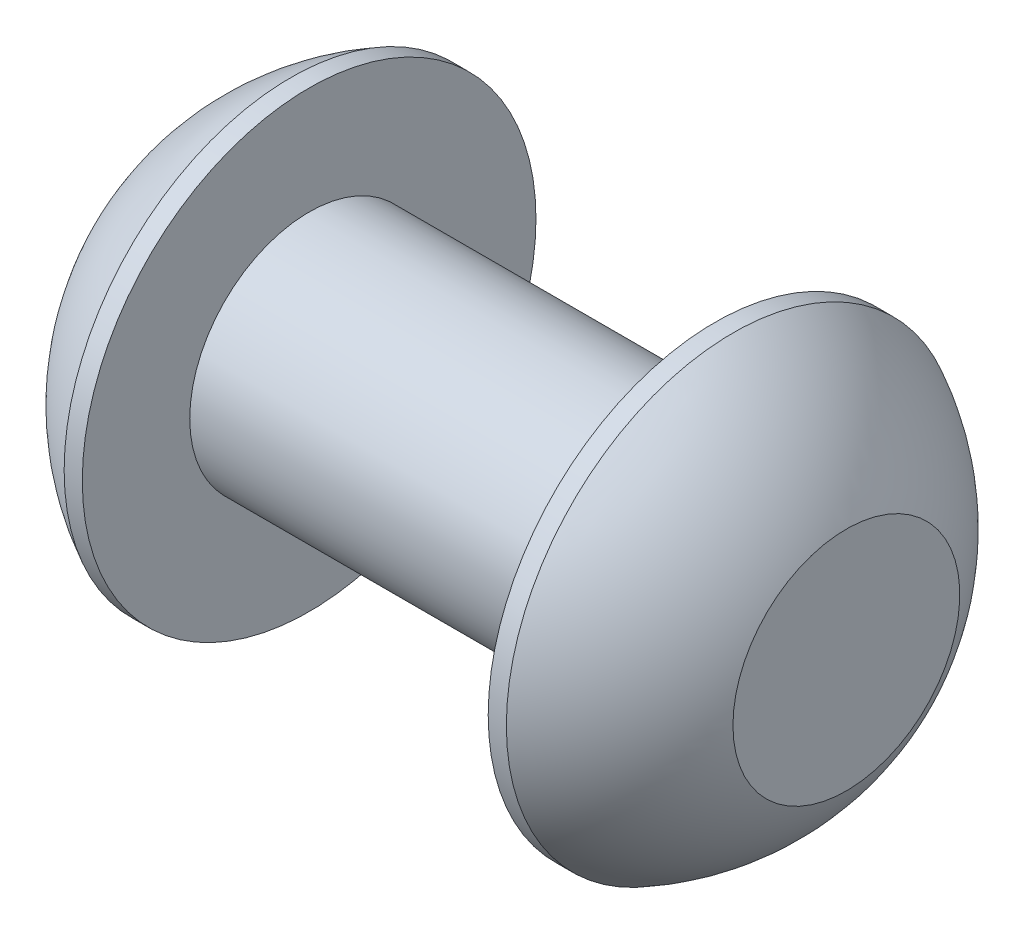
SolidWorks part; units mm, degrees
ref_plane "Front Plane" through (0, 0, 0) normal (0, 0, 1) x (1, 0, 0)
ref_plane "Top Plane" through (0, 0, 0) normal (0, 1, 0) x (1, 0, 0)
ref_plane "Right Plane" through (0, 0, 0) normal (1, 0, 0) x (0, 0, -1)
sketch "Sketch2" plane through (0, 0, 0) normal (0, 0, 1) x (1, 0, 0)
  line L0 (-1.1781, 0) -> (27.4341, 0) construction
  line L1 (11.25, 2.5) -> (2.75, 2.5)
  line L2 (2.75, 2.5) -> (2.75, 4.75)
  line L3 (2.75, 4.75) -> (2.37, 4.75)
  line L4 (0, 0) -> (14, 0) construction
  line L5 (2.75, -4.75) -> (2.37, -4.75) construction
  line L7 (14, 0) -> (0, 0)
  line L8 (0, 2.375) -> (0, -2.375) construction
  line L9 (0, 0) -> (0, 2.375)
  line L11 (11.695, -2.055) -> (11.25, -2.5) construction
  line L13 (2.75, 4.75) -> (2.75, 2.5) construction
  line L14 (11.25, 2.5) -> (11.25, 4.75)
  line L15 (11.25, 4.75) -> (11.63, 4.75)
  line L17 (14, 0) -> (14, 2.375)
  line L18 (11.25, 4.75) -> (11.63, 4.75)
  line L19 (11.25, 2.5) -> (11.25, 4.75)
  arc A0 (14, 2.375) -> (11.63, 4.75) centre (9.245, 0) ccw
  arc A1 (0, 2.375) -> (2.37, 4.75) centre (4.755, 0) cw
  dimension "D1" = 8.5
revolve "Revolve1" add sketch "Sketch2" angle 360 about L0
